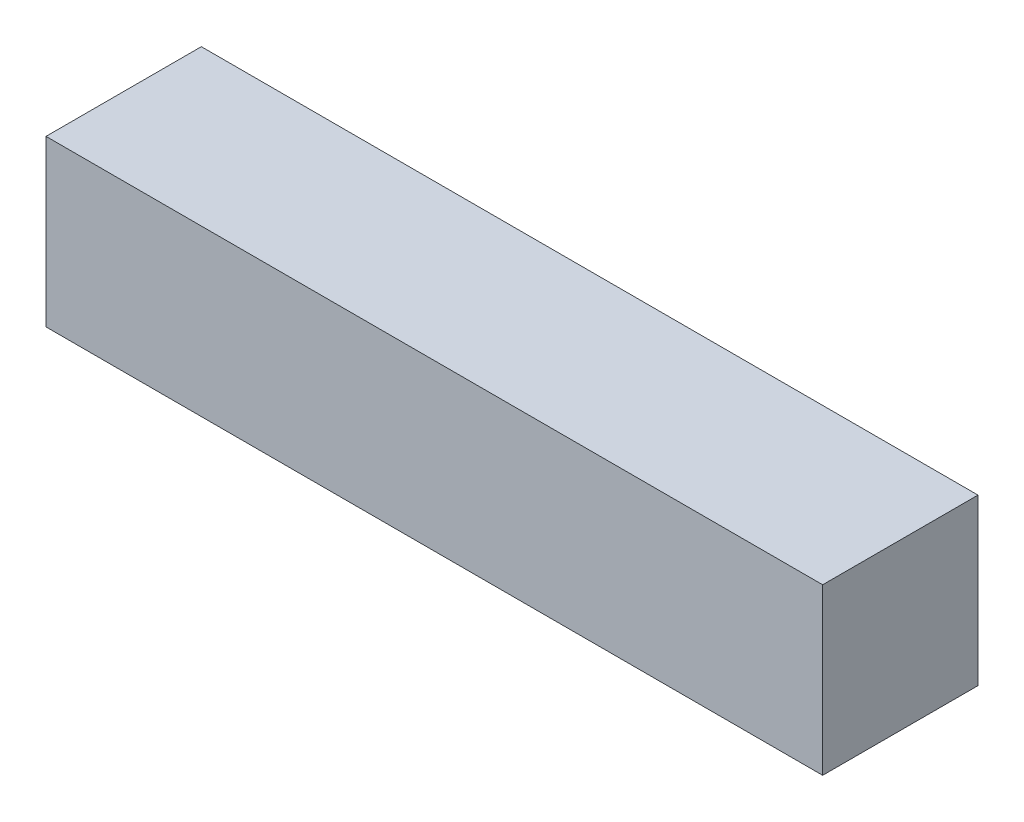
SolidWorks part; units mm, degrees
ref_plane "Front Plane" through (0, 0, 0) normal (0, 0, 1) x (1, 0, 0)
ref_plane "Top Plane" through (0, 0, 0) normal (0, 1, 0) x (1, 0, 0)
ref_plane "Right Plane" through (0, 0, 0) normal (1, 0, 0) x (0, 0, -1)
sketch "Sketch1" plane through (0, 0, 0) normal (0, 1, 0) x (1, 0, 0)
  line L1 (0, 0) -> (12192, 0)
  line L2 (0, 0) -> (0, -2438.4)
  line L3 (0, -2438.4) -> (12192, -2438.4)
  line L4 (12192, 0) -> (12192, -2438.4)
  dimension "D1" = 12192
  dimension "D2" = 2438.4
extrude "Boss-Extrude1" add sketch "Sketch1" along normal blind 2590.8
ref_plane "Plane1" through (76.2, 0, 0) normal (-1, 0, 0) x (0, 0, 1)
sketch "Sketch2" plane through (76.2, 0, 0) normal (-1, 0, 0) x (0, 0, 1)
  line L0 (0, 2590.8) -> (0, 0) construction
  line L1 (50.8, 2413) -> (2387.6, 2413)
  line L2 (50.8, 2413) -> (50.8, 177.8)
  line L3 (50.8, 177.8) -> (2387.6, 177.8)
  line L4 (2387.6, 2413) -> (2387.6, 177.8)
  line L5 (2438.4, 2590.8) -> (2438.4, 0) construction
  line L6 (0, 2590.8) -> (2438.4, 2590.8) construction
  line L7 (0, 0) -> (2438.4, 0) construction
  dimension "D1" = 50.8
  dimension "D2" = 50.8
  dimension "D3" = 177.8
  dimension "D4" = 177.8
extrude "Cut-Extrude1" cut sketch "Sketch2" against normal blind 12039.6
